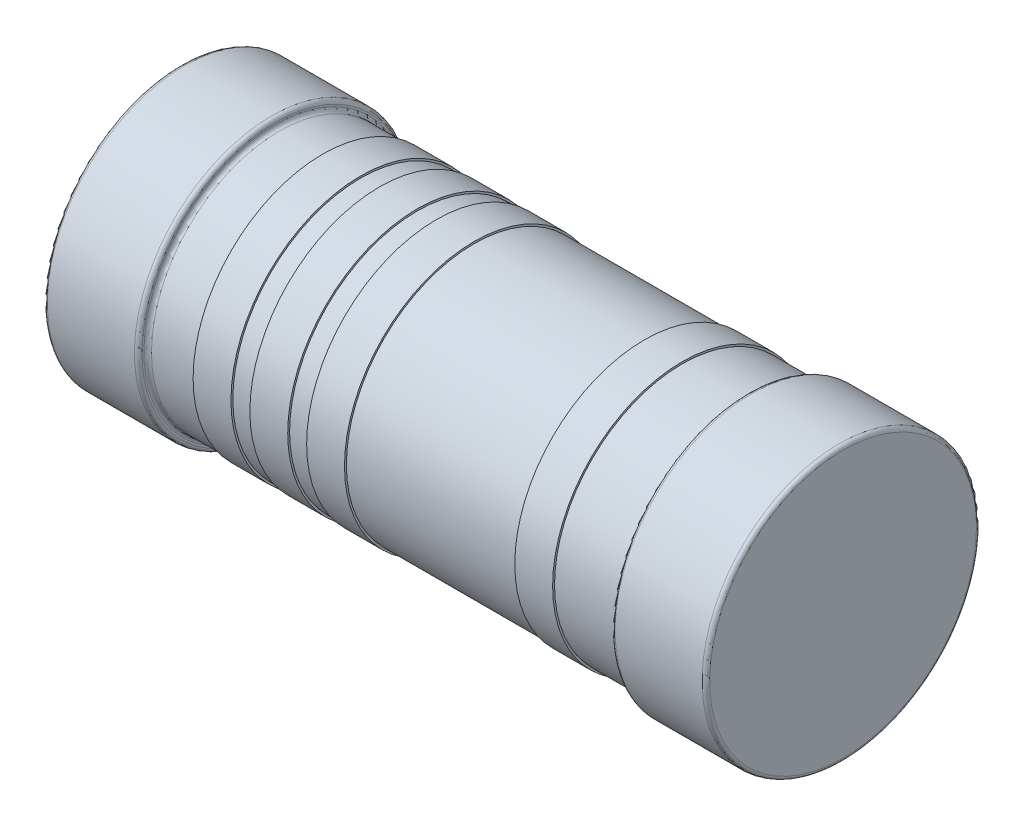
SolidWorks part; units mm, degrees
ref_plane "Front Plane" through (0, 0, 0) normal (0, 0, 1) x (1, 0, 0)
ref_plane "Top Plane" through (0, 0, 0) normal (0, 1, 0) x (1, 0, 0)
ref_plane "Right Plane" through (0, 0, 0) normal (1, 0, 0) x (0, 0, -1)
sketch "Sketch1" plane through (0, 0, 0) normal (0, 0, 1) x (1, 0, 0)
  line L0 (-1.75, 0.725) -> (1.75, 0.725)
  line L1 (0, 0) -> (0, 0.725) construction
  line L2 (-1.75, 0.725) -> (-3.0256, 0.725) construction
  line L3 (1.75, 0.725) -> (1.75, 0.02)
  line L4 (-1.73, 0) -> (-1.27, 0)
  line L5 (-1.75, 0.02) -> (-1.75, 0.725)
  line L6 (-1.25, 0.02) -> (-1.25, 0.03)
  line L7 (-1.23, 0.05) -> (-1, 0.05)
  line L8 (1.25, 0.03) -> (1.25, 0.02)
  line L9 (1.27, 0) -> (1.73, 0)
  line L10 (-1, 0.05) -> (-1, 0.04)
  line L11 (-1, 0.04) -> (-0.8, 0.04)
  line L12 (-0.8, 0.04) -> (-0.8, 0.05)
  line L13 (-0.7, 0.05) -> (-0.7, 0.04)
  line L14 (-0.7, 0.04) -> (-0.5, 0.04)
  line L15 (-0.5, 0.04) -> (-0.5, 0.05)
  line L16 (-0.2, 0.04) -> (-0.4, 0.04)
  line L17 (-0.4, 0.04) -> (-0.4, 0.05)
  line L18 (0.9, 0.05) -> (1.23, 0.05)
  line L19 (-0.2, 0.04) -> (-0.2, 0.05)
  line L20 (0.9, 0.05) -> (0.9, 0.04)
  line L21 (0.9, 0.04) -> (0.7, 0.04)
  line L22 (0.7, 0.04) -> (0.7, 0.05)
  line L23 (-0.9, 0.04) -> (-0.9, -0.0114) construction
  line L24 (-0.6, 0.04) -> (-0.6, -0.0114) construction
  line L25 (-0.3, 0.04) -> (-0.3, -0.0151) construction
  line L26 (0.8, 0.04) -> (0.8, -0.0151) construction
  line L27 (-0.2, 0.05) -> (0.7, 0.05)
  line L28 (-0.5, 0.05) -> (-0.4, 0.05)
  line L29 (-0.8, 0.05) -> (-0.7, 0.05)
  arc A0 (1.75, 0.02) -> (1.73, 0) centre (1.73, 0.02) cw
  arc A1 (1.27, 0) -> (1.25, 0.02) centre (1.27, 0.02) cw
  arc A2 (1.25, 0.03) -> (1.23, 0.05) centre (1.23, 0.03) ccw
  arc A3 (-1.23, 0.05) -> (-1.25, 0.03) centre (-1.23, 0.03) ccw
  arc A4 (-1.25, 0.02) -> (-1.27, 0) centre (-1.27, 0.02) cw
  arc A5 (-1.75, 0.02) -> (-1.73, 0) centre (-1.73, 0.02) ccw
  point P15 (1.75, 0)
  point P18 (1.25, 0)
  dimension "D5" = 0.02
  dimension "D1" = 3.5
  dimension "D2" = 0.5
  dimension "D3" = 0.05
  dimension "D4" = 0.725
  dimension "D6" = 0.2
  dimension "D7" = 0.01
  dimension "D8" = 0.3
  dimension "D9" = 0.3
  dimension "D10" = 0.3
  dimension "D11" = 0.8
revolve "Revolve1" add sketch "Sketch1" angle 360 about L2
